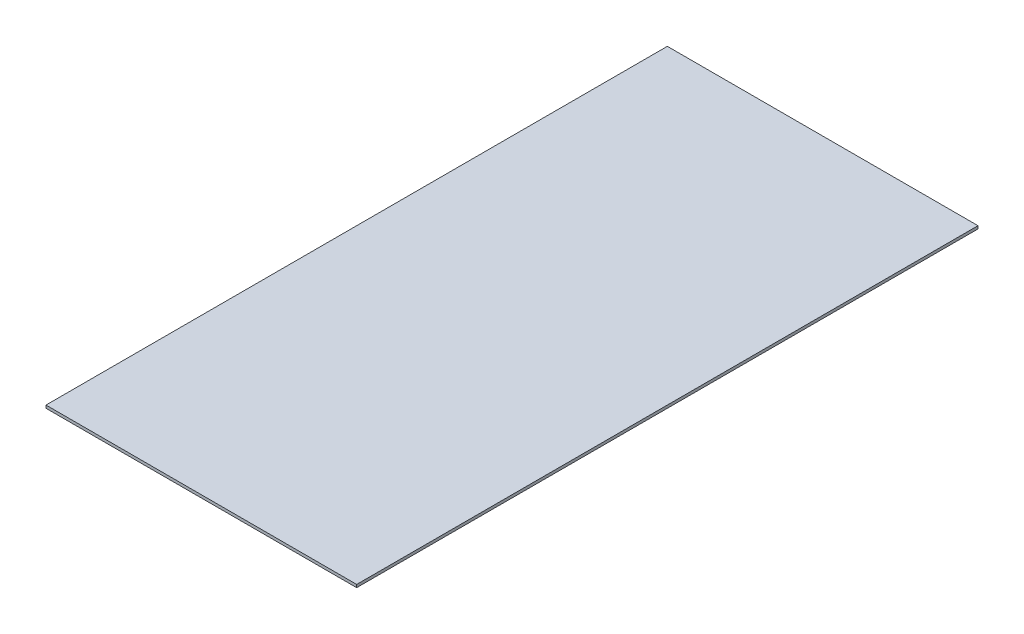
SolidWorks part; units mm, degrees
material "Teak"
ref_plane "Front Plane" through (0, 0, 0) normal (0, 0, 1) x (1, 0, 0)
ref_plane "Top Plane" through (0, 0, 0) normal (0, 1, 0) x (1, 0, 0)
ref_plane "Right Plane" through (0, 0, 0) normal (1, 0, 0) x (0, 0, -1)
sketch "Sketch1" plane through (0, 0, 0) normal (0, 1, 0) x (1, 0, 0)
  line L1 (-304.8, -609.6) -> (304.8, -609.6)
  line L2 (-304.8, -609.6) -> (-304.8, 609.6)
  line L3 (-304.8, 609.6) -> (304.8, 609.6)
  line L4 (304.8, -609.6) -> (304.8, 609.6)
  line L5 (-304.8, -609.6) -> (304.8, 609.6) construction
  line L6 (-304.8, 609.6) -> (304.8, -609.6) construction
  point P0 (0, 0)
  dimension "D1" = 609.6
  dimension "D2" = 1219.2
extrude "Boss-Extrude1" add sketch "Sketch1" along normal blind 5.5562
